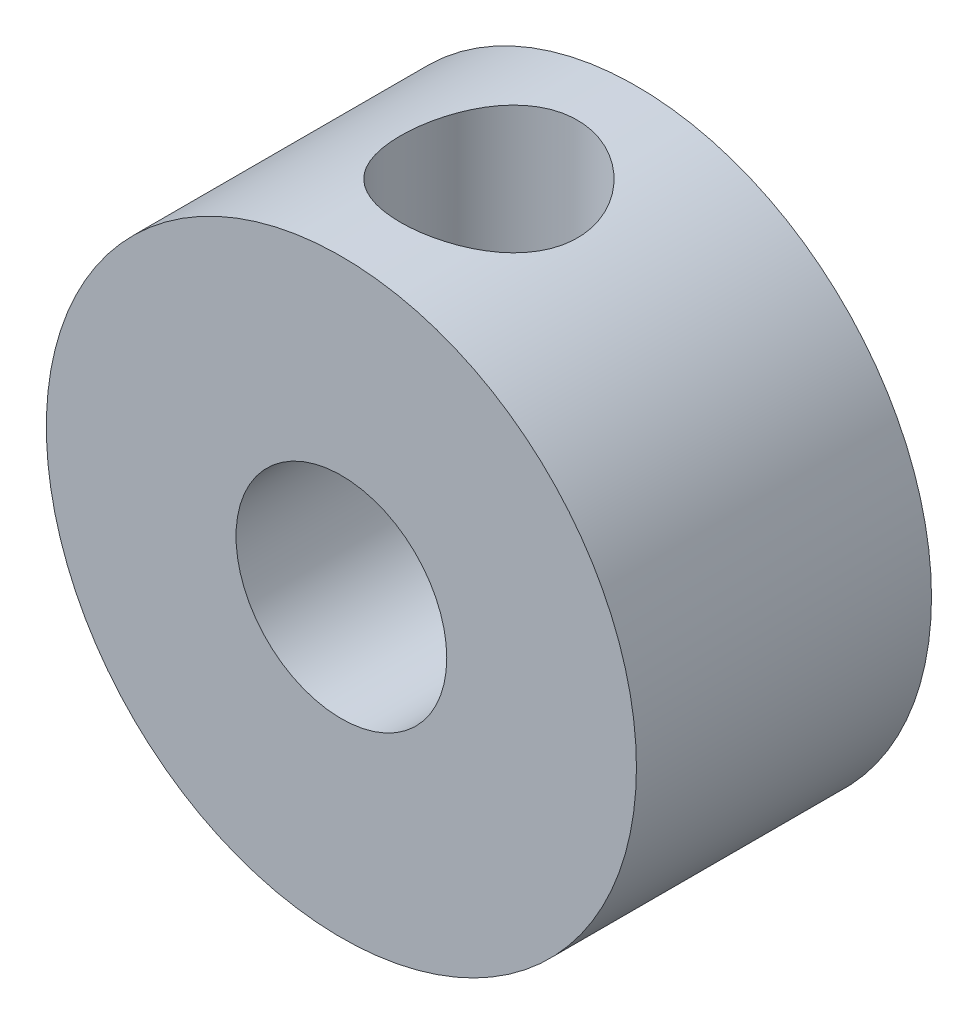
SolidWorks part; units mm, degrees
material "Plain Carbon Steel"
ref_plane "Front Plane" through (0, 0, 0) normal (0, 0, 1) x (1, 0, 0)
ref_plane "Top Plane" through (0, 0, 0) normal (0, 1, 0) x (1, 0, 0)
ref_plane "Right Plane" through (0, 0, 0) normal (1, 0, 0) x (0, 0, -1)
sketch "Sketch1" plane through (0, 0, 0) normal (0, 0, 1) x (1, 0, 0)
  circle A0 centre (0, 0) radius 2.5
  circle A1 centre (0, 0) radius 7
  dimension "D1" = 5
  dimension "D2" = 14
extrude "Boss-Extrude1" add sketch "Sketch1" along normal blind 7
ref_plane "Plane1" through (0, 7, 0) normal (0, 1, 0) x (1, 0, 0)
hole_wizard "M5x0.8 Tapped Hole1" positions "Sketch3" profile "Sketch2" tap size "M5x0.8" standard "ANSI Metric"
sketch "Sketch3" plane through (0, 7, 0) normal (0, 1, 0) x (1, 0, 0)
  line L0 (0, 0) -> (0, -7) construction
  line L1 (-7, -7) -> (7, -7) construction
  point P8 (0, -3.5)
sketch "Sketch2" plane through (0, 7, 3.5) normal (1, 0, 0) x (0, 0, 1)
  line L0 (0, 0) -> (0, 4.5)
  line L1 (0, 4.5) -> (2.1, 4.5)
  line L2 (2.1, 4.5) -> (2.1, 0)
  line L5 (2.1, 0) -> (0, 0)
  line L11 (0, -6.35) -> (0, 107.95) construction
  dimension "Thread Major Dia." = 4.2
  dimension "Thru Tap Drill Depth" = 4.5
